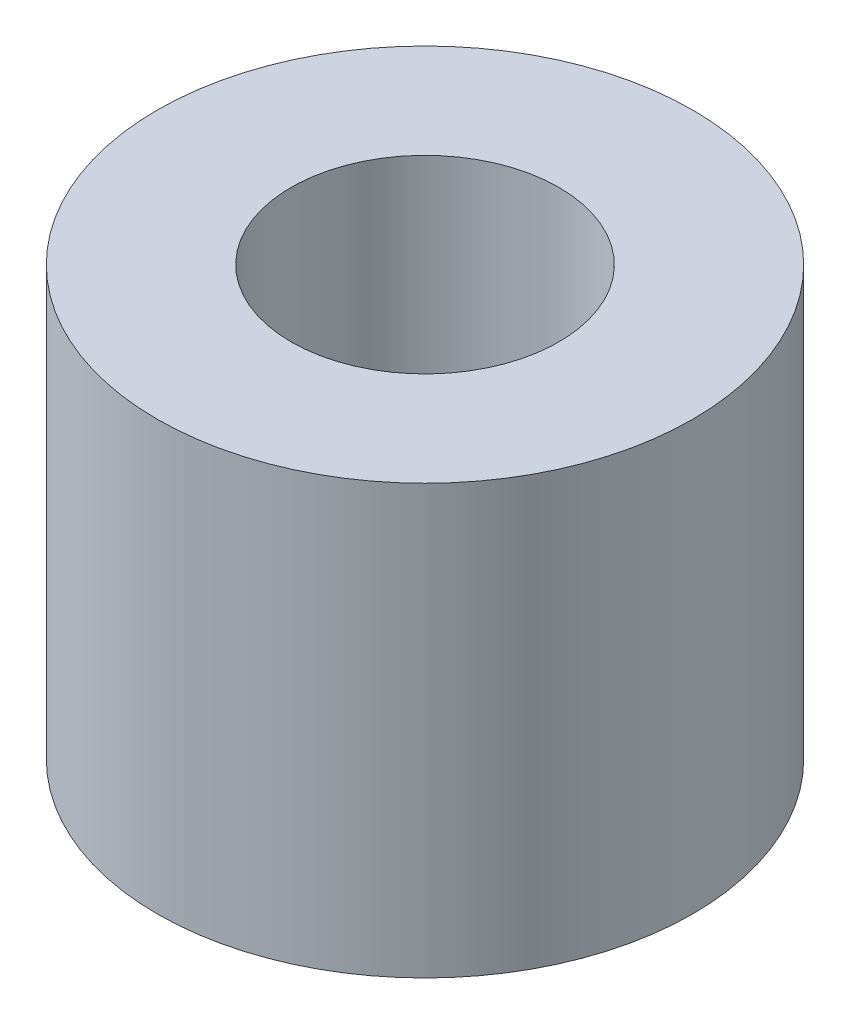
SolidWorks part; units mm, degrees
material "6061-T6 (SS)"
ref_plane "Front Plane" through (0, 0, 0) normal (0, 0, 1) x (1, 0, 0)
ref_plane "Top Plane" through (0, 0, 0) normal (0, 1, 0) x (1, 0, 0)
ref_plane "Right Plane" through (0, 0, 0) normal (1, 0, 0) x (0, 0, -1)
sketch "Sketch1" plane through (0, 0, 0) normal (0, 1, 0) x (1, 0, 0)
  circle A0 centre (0, 0) radius 6.35
  circle A1 centre (0, 0) radius 3.175
  dimension "D1" = 12.7
  dimension "D2" = 6.35
extrude "Boss-Extrude1" add sketch "Sketch1" along normal blind 10.16
